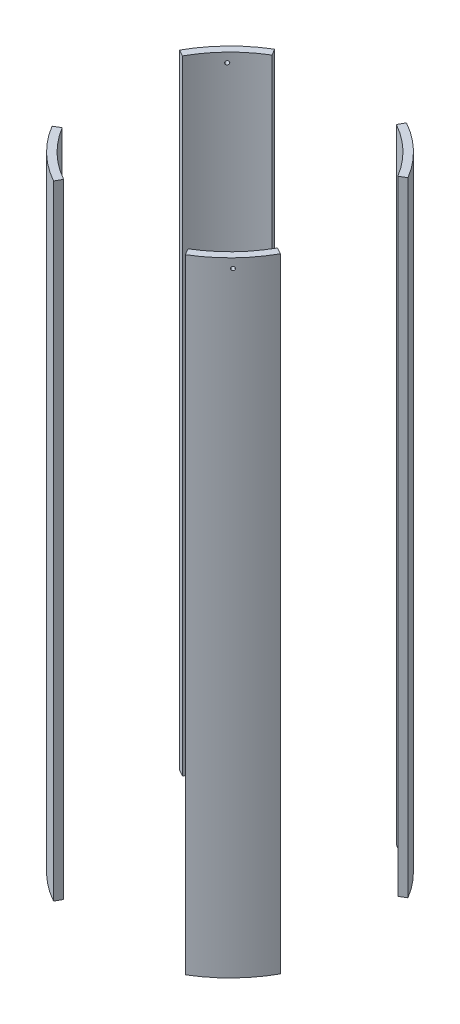
SolidWorks part; units mm, degrees
material "6061-T6 (SS)"
ref_plane "Front Plane" through (0, 0, 0) normal (0, 0, 1) x (1, 0, 0)
ref_plane "Top Plane" through (0, 0, 0) normal (0, 1, 0) x (1, 0, 0)
ref_plane "Right Plane" through (0, 0, 0) normal (1, 0, 0) x (0, 0, -1)
sketch "Sketch2" plane through (0, 0, 0) normal (0, 1, 0) x (1, 0, 0)
  circle A0 centre (0, 0) radius 88.9
  circle A1 centre (0, 0) radius 83.82
  dimension "D1" = 177.8
  dimension "D2" = 167.64
extrude "Boss-Extrude1" add sketch "Sketch2" along normal mid plane 427.355
sketch "Sketch3" plane through (0, 0, 0) normal (0, 1, 0) x (1, 0, 0)
  line L0 (0, 0) -> (169.6618, 101.6776)
  line L1 (-58.1167, 96.9749) -> (0, 0)
  line L2 (0, 0) -> (53.9, 96.9749)
  line L3 (53.9, 96.9749) -> (-58.1167, 96.9749)
  line L4 (0, 0) -> (70.9917, -118.4586)
  line L5 (70.9917, -118.4586) -> (-65.8409, -118.4586)
  line L6 (-65.8409, -118.4586) -> (0, 0)
  line L7 (169.6618, 101.6776) -> (169.6618, -94.3004)
  line L8 (169.6618, -94.3004) -> (0, 0)
  line L9 (0, 0) -> (-123.7413, 68.7771)
  line L10 (-123.7413, 68.7771) -> (-123.7413, -74.1577)
  line L11 (-123.7413, -74.1577) -> (0, 0)
  dimension "D1" = 60
  dimension "D2" = 60
  dimension "D3" = 60
  dimension "D4" = 60
  dimension "D5" = 30
  dimension "D6" = 30
extrude "Cut-Extrude1" cut sketch "Sketch3" against normal through all both and the other way through all contours L8 L7 L0 | L2 L3 L1 | L10 L11 L9 | L6 L5 L4
ref_plane "Bolt reference plane" through (-56.3092, 0, 58.1758) normal (0.6955, 0, -0.7185) x (-0.7185, 0, -0.6955)
sketch "Sketch5" plane through (-56.3092, 0, 58.1758) normal (0.6955, 0, -0.7185) x (-0.7185, 0, -0.6955)
  circle A0 centre (-0.0228, 207.3275) radius 1.27
  dimension "D1" = 2.54
  dimension "D2" = 21.717
  dimension "D3" = 6.35
extrude "Top bolt holes" cut sketch "Sketch5" against normal through all
sketch "Sketch6" plane through (0, -213.6775, 0) normal (0, -1, 0) x (-1, 0, 0)
  line L0 (71.8974, -43.0878) -> (40.7211, -73.2638) construction
  line L1 (0, 0) -> (61.8287, -63.8782) construction
  circle A0 centre (60.0621, -62.0531) radius 1.27
  arc A1 (43.189, -77.7041) -> (76.2548, -45.6992) centre (0, 0) ccw construction
  dimension "D2" = 2.54
  dimension "D1" = 86.36
extrude "Bottom bolt holes" cut sketch "Sketch6" against normal blind 31.75
pattern_circular "Bolt pattern" count 4 over 360 about axis through (0, 0, 0) along (0, 1, 0) of "Top bolt holes", "Bottom bolt holes"
equation "\"D1@Boss-Extrude1\"=3*12"
